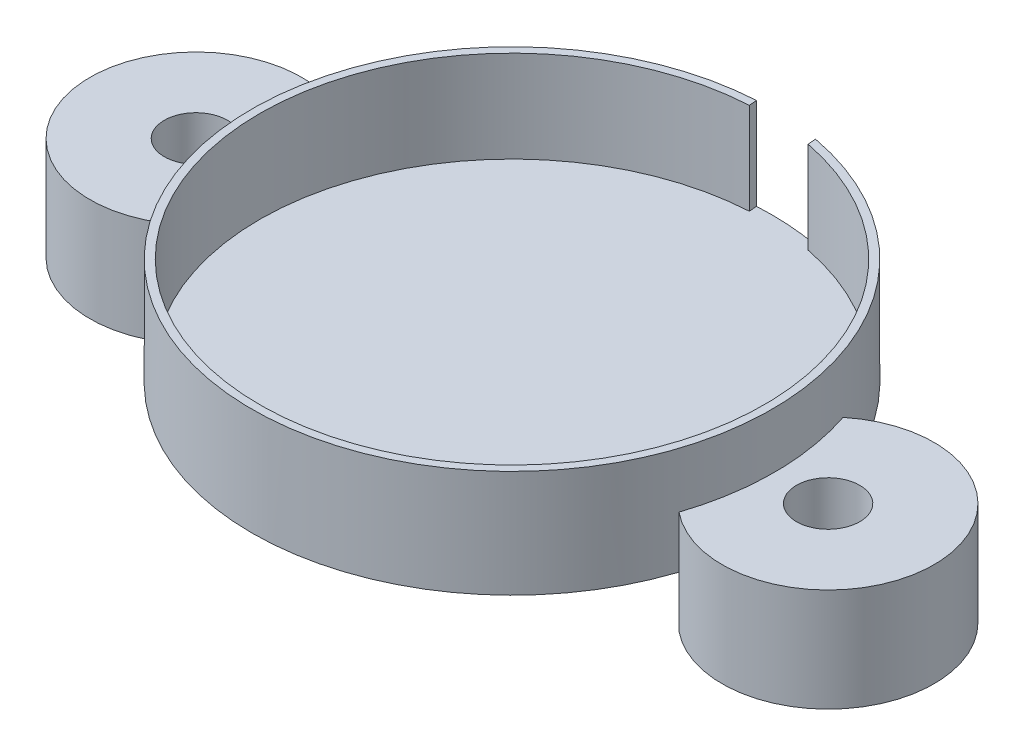
SolidWorks part; units mm, degrees
ref_plane "Front Plane" through (0, 0, 0) normal (0, 0, 1) x (1, 0, 0)
ref_plane "Top Plane" through (0, 0, 0) normal (0, 1, 0) x (1, 0, 0)
ref_plane "Right Plane" through (0, 0, 0) normal (1, 0, 0) x (0, 0, -1)
sketch "Sketch1" plane through (0, 0, 0) normal (0, 1, 0) x (1, 0, 0)
  circle A0 centre (0, 0) radius 53.2892
  dimension "D1" = 106.5784
extrude "Boss-Extrude1" add sketch "Sketch1" along normal blind 21.971 contours A0
sketch "Sketch3" plane through (0, 21.971, 0) normal (0, 1, 0) x (1, 0, 0)
  circle A0 centre (0, 0) radius 51.689
  dimension "D1" = 103.378
extrude "Cut-Extrude2" cut sketch "Sketch3" against normal blind 18.796
sketch "Sketch6" plane through (0, 21.971, 0) normal (0, 1, 0) x (1, 0, 0)
  line L0 (9.9549, 50.7213) -> (9.7919, 52.3819)
  line L1 (-2.969, 51.6037) -> (-3.1044, 53.1987)
  arc A0 (9.7919, 52.3819) -> (-3.1044, 53.1987) centre (0, 0) ccw
  circle A1 centre (0, 0) radius 53.2892 construction
  circle A2 centre (0, 0) radius 53.2892 construction
  arc A3 (9.9549, 50.7213) -> (-2.969, 51.6037) centre (0, 0) ccw
  circle A4 centre (0, 0) radius 51.689 construction
  point P12 (0, 53.2892)
  point P13 (0, 51.7225)
  point P14 (-2.969, 51.6037)
  point P15 (-2.969, 52.3819)
  dimension "D1" = 12.954
  dimension "D2" = 12.954
extrude "Cut-Extrude7" cut sketch "Sketch6" against normal blind 18.796
sketch "Sketch7" plane through (0, 0, 0) normal (0, -1, 0) x (1, 0, 0)
  arc A7 (51.0212, -16.8107) -> (51.0212, 16.8107) centre (64.77, 0) ccw
  arc A8 (-51.0212, 16.8107) -> (-51.0212, -16.8107) centre (-64.77, 0) ccw
  circle A9 centre (-64.77, 0) radius 6.477
  circle A10 centre (64.77, 0) radius 6.477
  arc A12 (-51.0212, -16.8107) -> (-51.0212, 16.8107) centre (-0.4664, 0) cw
  arc A13 (51.0212, 16.8107) -> (51.0212, -16.8107) centre (0.4664, 0) cw
  dimension "D4" = 43.434
  dimension "D5" = 12.954
  dimension "D6" = 12.954
  dimension "D1" = 43.434
extrude "Boss-Extrude3" add sketch "Sketch7" against normal blind 10.9855 and the other way blind 10.16
